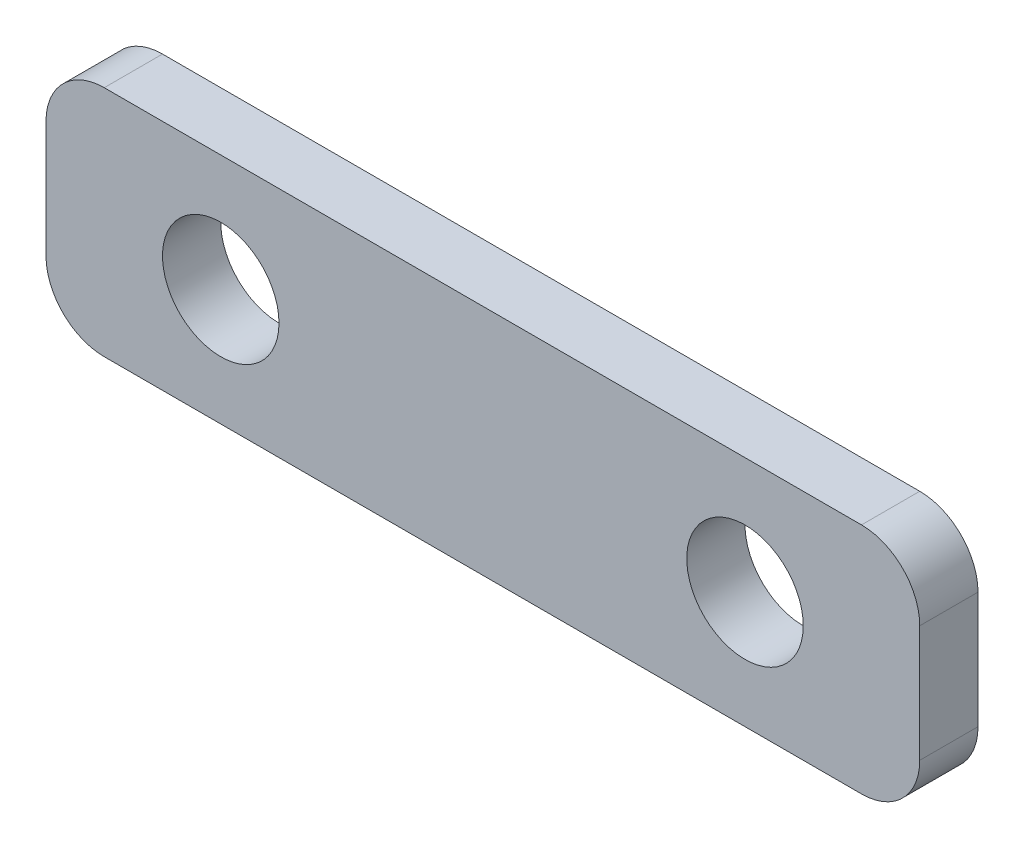
SolidWorks part; units mm, degrees
ref_plane "Front Plane" through (0, 0, 0) normal (0, 0, 1) x (1, 0, 0)
ref_plane "Top Plane" through (0, 0, 0) normal (0, 1, 0) x (1, 0, 0)
ref_plane "Right Plane" through (0, 0, 0) normal (1, 0, 0) x (0, 0, -1)
sketch "Sketch1" plane through (0, 0, 0) normal (0, 0, 1) x (1, 0, 0)
  line L0 (-200, 151.7559) -> (-170, 151.7559) construction
  line L2 (-190, 151.7559) -> (-60, 151.7559)
  line L3 (-200, 141.7559) -> (-200, 121.7559)
  line L4 (-190, 111.7559) -> (-60, 111.7559)
  line L5 (-50, 141.7559) -> (-50, 121.7559)
  line L6 (-200, 151.7559) -> (-50, 111.7559) construction
  line L7 (-200, 111.7559) -> (-50, 151.7559) construction
  line L8 (-50, 151.7559) -> (-80, 151.7559) construction
  line L9 (-170, 151.7559) -> (-170, 111.7559) construction
  line L10 (-80, 151.7559) -> (-80, 111.7559) construction
  arc A0 (-60, 111.7559) -> (-50, 121.7559) centre (-60, 121.7559) ccw
  arc A1 (-60, 151.7559) -> (-50, 141.7559) centre (-60, 141.7559) cw
  arc A2 (-200, 121.7559) -> (-190, 111.7559) centre (-190, 121.7559) ccw
  arc A3 (-190, 151.7559) -> (-200, 141.7559) centre (-190, 141.7559) ccw
  circle A4 centre (-170, 131.7559) radius 10
  circle A5 centre (-80, 131.7559) radius 10
  point P0 (-125, 131.7559)
  dimension "D3" = 10
  dimension "D1" = 150
  dimension "D2" = 40
extrude "Boss-Extrude1" add sketch "Sketch1" along normal mid plane 10
